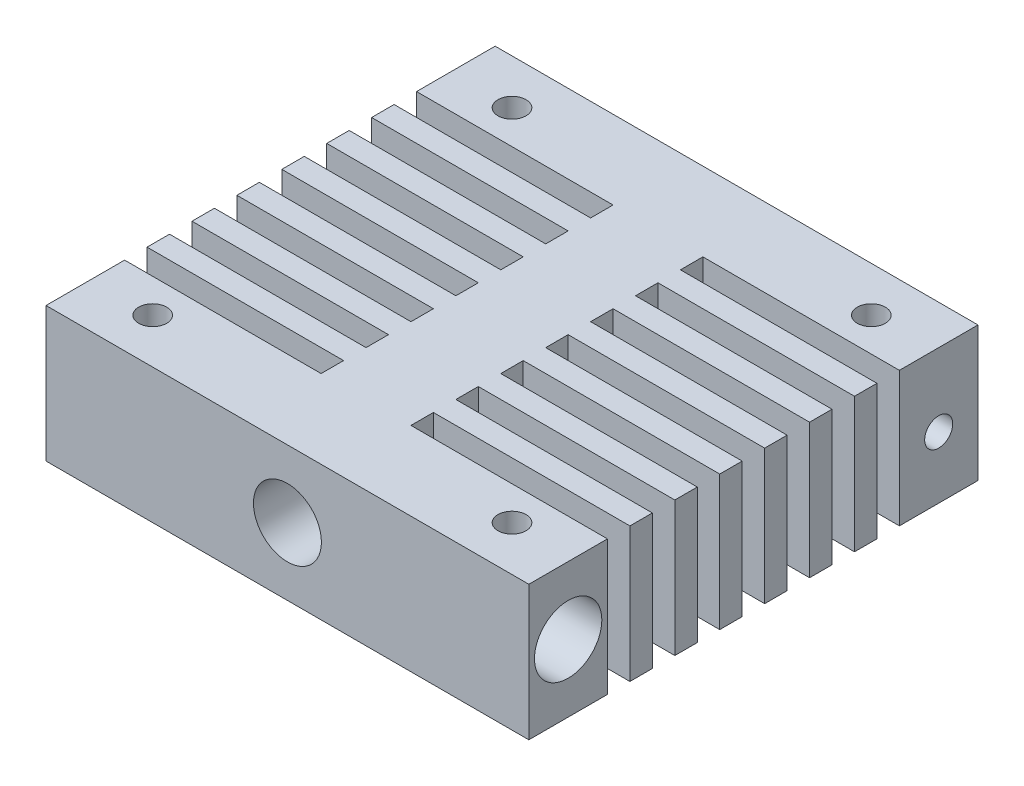
SolidWorks part; units mm, degrees
material "6063-O"
ref_plane "前视基准面" through (0, 0, 0) normal (0, 0, 1) x (1, 0, 0)
ref_plane "上视基准面" through (0, 0, 0) normal (0, 1, 0) x (1, 0, 0)
ref_plane "右视基准面" through (0, 0, 0) normal (1, 0, 0) x (0, 0, -1)
sketch "草图1" plane through (0, 0, 0) normal (0, 1, 0) x (1, 0, 0)
  line L0 (-123.0659, 0) -> (151.55, 0) construction
  line L1 (0, 104.9894) -> (0, -121.0574) construction
  line L2 (-21.5, 20) -> (-21.5, -20)
  line L3 (-21.5, -20) -> (21.5, -20)
  line L4 (21.5, -20) -> (21.5, 20)
  line L5 (21.5, 20) -> (-21.5, 20)
  dimension "D1" = 43
  dimension "D2" = 40
extrude "凸台-拉伸1" add sketch "草图1" along normal blind 2
sketch "草图2" plane through (0, 0, 0) normal (0, 1, 0) x (1, 0, 0)
  line L0 (51.1159, 0) -> (-53.8356, 0) construction
  line L1 (0, 43.0666) -> (0, -46.7433) construction
  line L2 (6, 20) -> (6, 16.51)
  line L3 (21.5, 20) -> (-21.5, 20) construction
  line L4 (6, 16.51) -> (-6, 16.51)
  line L5 (-6, 16.51) -> (-6, 20)
  line L6 (-6, 20) -> (6, 20)
  line L7 (-6, -20) -> (6, -20)
  line L8 (-6, -16.51) -> (-6, -20)
  line L9 (6, -16.51) -> (-6, -16.51)
  line L10 (6, -20) -> (6, -16.51)
  dimension "D1" = 12
  dimension "D2" = 33.02
extrude "凸台-拉伸2" [suppressed] add sketch "草图2" against normal blind 3
chamfer "倒角1" [suppressed] distance 0.5 angle 45
chamfer "倒角2" [suppressed] distance 0.2 angle 45
sketch "草图3" plane through (0, 2, 0) normal (0, 1, 0) x (1, 0, 0)
  line L0 (0, 34.8618) -> (0, -39.6513) construction
  line L1 (-44.5227, 0) -> (51.9212, 0) construction
  line L2 (-21.5, 20) -> (-21.5, -20)
  line L3 (-21.5, -20) -> (21.5, -20)
  line L4 (21.5, -20) -> (21.5, 20)
  line L5 (21.5, 20) -> (-21.5, 20)
  line L7 (21.5, 20) -> (-21.5, 20) construction
  line L8 (-21.5, -20) -> (21.5, -20) construction
  dimension "D1" = 43
extrude "凸台-拉伸3" add sketch "草图3" along normal blind 10
sketch "草图4" plane through (0, 0, 20) normal (0, 0, 1) x (1, 0, 0)
  circle A0 centre (0, 6) radius 3.025
  dimension "D2" = 6.05
  dimension "D1" = 6
extrude "切除-拉伸1" cut sketch "草图4" against normal blind 20
sketch "草图5" plane through (0, 0, -20) normal (0, 0, -1) x (-1, 0, 0)
  circle A0 centre (0, 6) radius 2.025
  dimension "D1" = 4.05
extrude "切除-拉伸2" cut sketch "草图5" against normal up to next
hole_wizard "M6 螺纹孔1" positions "草图6" profile "草图7" tap size "M6" standard "GB"
sketch "草图6" plane through (0, 0, -20) normal (0, 0, -1) x (-1, 0, 0)
  point P0 (0, 6)
sketch "草图7" plane through (0, 6, -20) normal (1, 0, 0) x (0, 1, 0)
  line L0 (0, 0) -> (0, 8)
  line L1 (0, 8) -> (2.5, 8)
  line L2 (2.5, 8) -> (2.5, 0)
  line L5 (2.5, 0) -> (0, 0)
  line L10 (0, 8) -> (-2.5, 8) construction
  line L11 (0, -6.35) -> (0, 107.95) construction
  dimension "螺纹孔钻头直径" = 5
  dimension "螺纹孔钻头深度" = 8
  dimension "导头角度" = 180
cosmetic thread "孔螺蚊线1" parameters "D1"=8, "D2"=6
sketch "草图8" plane through (0, 12, 0) normal (0, 1, 0) x (1, 0, 0)
  line L0 (-21.5, -13) -> (-4, -13)
  line L1 (-4, -13) -> (-4, -11)
  line L2 (-4, -11) -> (-21.5, -11)
  line L3 (-21.5, -11) -> (-21.5, -13)
  line L4 (0, 25.0591) -> (0, -36.4121) construction
  line L6 (-21.5, -20) -> (21.5, -20) construction
  line L7 (-21.5, -9) -> (-4, -9)
  line L8 (-4, -7) -> (-21.5, -7)
  line L9 (-21.5, -7) -> (-21.5, -9)
  line L10 (-4, -9) -> (-4, -7)
  line L11 (-21.5, -5) -> (-4, -5)
  line L12 (-4, -3) -> (-21.5, -3)
  line L13 (-21.5, -3) -> (-21.5, -5)
  line L14 (-4, -5) -> (-4, -3)
  line L15 (-21.5, -1) -> (-4, -1)
  line L16 (-4, 1) -> (-21.5, 1)
  line L17 (-21.5, 1) -> (-21.5, -1)
  line L18 (-4, -1) -> (-4, 1)
  line L19 (-21.5, 3) -> (-4, 3)
  line L20 (-4, 5) -> (-21.5, 5)
  line L21 (-21.5, 5) -> (-21.5, 3)
  line L22 (-4, 3) -> (-4, 5)
  line L23 (-21.5, 7) -> (-4, 7)
  line L24 (-4, 9) -> (-21.5, 9)
  line L25 (-21.5, 9) -> (-21.5, 7)
  line L26 (-4, 7) -> (-4, 9)
  line L27 (-21.5, 11) -> (-4, 11)
  line L28 (-4, 13) -> (-21.5, 13)
  line L29 (-21.5, 13) -> (-21.5, 11)
  line L30 (-4, 11) -> (-4, 13)
  line L31 (4, 11) -> (4, 13)
  line L32 (21.5, 13) -> (21.5, 11)
  line L33 (4, 13) -> (21.5, 13)
  line L34 (21.5, 11) -> (4, 11)
  line L35 (-21.5, 20) -> (-21.5, -20) construction
  line L45 (4, 7) -> (4, 9)
  line L46 (21.5, 9) -> (21.5, 7)
  line L47 (4, 9) -> (21.5, 9)
  line L48 (21.5, 7) -> (4, 7)
  line L49 (4, 3) -> (4, 5)
  line L50 (21.5, 5) -> (21.5, 3)
  line L51 (4, 5) -> (21.5, 5)
  line L52 (21.5, 3) -> (4, 3)
  line L53 (4, -1) -> (4, 1)
  line L54 (21.5, 1) -> (21.5, -1)
  line L55 (4, 1) -> (21.5, 1)
  line L56 (21.5, -1) -> (4, -1)
  line L57 (4, -5) -> (4, -3)
  line L58 (21.5, -3) -> (21.5, -5)
  line L59 (4, -3) -> (21.5, -3)
  line L60 (21.5, -5) -> (4, -5)
  line L61 (4, -9) -> (4, -7)
  line L62 (21.5, -7) -> (21.5, -9)
  line L63 (4, -7) -> (21.5, -7)
  line L64 (21.5, -9) -> (4, -9)
  line L65 (21.5, -11) -> (21.5, -13)
  line L66 (4, -11) -> (21.5, -11)
  line L67 (4, -13) -> (4, -11)
  line L68 (21.5, -13) -> (4, -13)
  dimension "D1" = 2
  dimension "D2" = 7
  dimension "D3" = 8
  dimension "D5" = 2
  dimension "D4" = 7
extrude "切除-拉伸3" cut sketch "草图8" against normal up to surface (12 mm away) up to face at (0, 0, 0)
hole_wizard "M3 螺纹孔1" positions "草图9" profile "草图10" tap size "M3" standard "GB" end condition through all
sketch "草图9" plane through (0, 12, 0) normal (0, 1, 0) x (1, 0, 0)
  point P0 (-16, 16)
  point P2 (16, 16)
  point P6 (-16, -16)
  point P16 (16, -16)
  dimension "D1" = 16
  dimension "D2" = 16
  dimension "D3" = 16
  dimension "D4" = 16
cosmetic thread "孔螺蚊线11" parameters "D2"=3
cosmetic thread "孔螺蚊线12" parameters "D2"=3
cosmetic thread "孔螺蚊线13" parameters "D2"=3
cosmetic thread "孔螺蚊线14" parameters "D2"=3
sketch "草图10" plane through (-16, 12, -16) normal (1, 0, 0) x (0, 0, 1)
  line L0 (0, 0) -> (0, 12)
  line L1 (0, 12) -> (1.25, 12)
  line L2 (1.25, 12) -> (1.25, 0)
  line L5 (1.25, 0) -> (0, 0)
  line L11 (0, -6.35) -> (0, 107.95) construction
  dimension "通孔螺纹孔钻头直径" = 2.5
  dimension "通孔螺纹孔钻头深度" = 12
hole_wizard "M3 螺纹孔2" positions "草图12" profile "草图13" tap size "M3" standard "GB"
sketch "草图12" plane through (21.5, 0, 0) normal (1, 0, 0) x (0, 0, -1)
  line L2 (20, 12) -> (20, 0) construction
  line L3 (13, 0) -> (20, 0) construction
  point P0 (16.5, 5.5)
  dimension "D1" = 3.5
  dimension "D2" = 5.5
sketch "草图13" plane through (21.5, 5.5, -16.5) normal (0, 1, 0) x (0, 0, -1)
  line L0 (0, 0) -> (0, 4)
  line L1 (0, 4) -> (1.25, 4)
  line L2 (1.25, 4) -> (1.25, 0)
  line L5 (1.25, 0) -> (0, 0)
  line L10 (0, 4) -> (-1.25, 4) construction
  line L11 (0, -6.35) -> (0, 107.95) construction
  dimension "螺纹孔钻头直径" = 2.5
  dimension "螺纹孔钻头深度" = 4
  dimension "导头角度" = 180
cosmetic thread "孔螺蚊线6" parameters "D1"=4, "D2"=3
hole_wizard "M3 螺纹孔3" positions "草图14" profile "草图15" tap size "M3" standard "GB"
sketch "草图14" plane through (-21.5, 0, 0) normal (-1, 0, 0) x (0, 0, 1)
  line L3 (-20, 12) -> (-20, 0) construction
  line L4 (-20, 0) -> (-13, 0) construction
  line L5 (13, 0) -> (20, 0) construction
  line L6 (20, 12) -> (20, 0) construction
  point P0 (-16.5, 5.5)
  point P8 (16.5, 5.5)
  dimension "D1" = 3.5
  dimension "D2" = 5.5
  dimension "D3" = 5.5
  dimension "D4" = 3.5
sketch "草图15" plane through (-21.5, 5.5, -16.5) normal (0, 1, 0) x (0, 0, 1)
  line L0 (0, 0) -> (0, 4)
  line L1 (0, 4) -> (1.25, 4)
  line L2 (1.25, 4) -> (1.25, 0)
  line L5 (1.25, 0) -> (0, 0)
  line L10 (0, 4) -> (-1.25, 4) construction
  line L11 (0, -6.35) -> (0, 107.95) construction
  dimension "螺纹孔钻头直径" = 2.5
  dimension "螺纹孔钻头深度" = 4
  dimension "导头角度" = 180
cosmetic thread "孔螺蚊线7" parameters "D1"=4, "D2"=3
cosmetic thread "孔螺蚊线16" parameters "D1"=4, "D2"=3
sketch "草图16" plane through (21.5, 0, 0) normal (1, 0, 0) x (0, 0, -1)
  line L3 (-20, 0) -> (-13, 0) construction
  line L4 (-20, 12) -> (-20, 0) construction
  circle A0 centre (-16.5, 6) radius 3
  dimension "D1" = 6
  dimension "D2" = 6
  dimension "D3" = 3.5
extrude "切除-拉伸4" cut sketch "草图16" against normal blind 13.5
hole_wizard "M3 螺纹孔4" positions "草图17" profile "草图18" tap size "M3" standard "GB"
sketch "草图17" plane through (8, 0, 0) normal (1, 0, 0) x (0, 0, -1)
  point P0 (-16.5, 6)
sketch "草图18" plane through (8, 6, 16.5) normal (0, 1, 0) x (0, 0, -1)
  line L0 (0, 0) -> (0, 4.975)
  line L1 (0, 4.975) -> (1.25, 4.975)
  line L2 (1.25, 4.975) -> (1.25, 0)
  line L5 (1.25, 0) -> (0, 0)
  line L11 (0, -6.35) -> (0, 107.95) construction
  dimension "通孔螺纹孔钻头直径" = 2.5
  dimension "通孔螺纹孔钻头深度" = 4.975
cosmetic thread "孔螺蚊线15" parameters "D2"=3
hole_wizard "M3 螺纹孔5" [suppressed] positions "草图19" profile "草图20" tap size "M3" standard "GB"
sketch "草图19" plane through (0, 0, 0) normal (0, -1, 0) x (-1, 0, 0)
  line L0 (0, 104.9894) -> (0, -121.0574) construction
  line L1 (123.0659, 0) -> (-151.55, 0) construction
  line L2 (0, 104.9894) -> (0, -121.0574) construction
  line L3 (123.0659, 0) -> (-151.55, 0) construction
  point P0 (-16, 16.5)
  point P2 (16, 16.5)
  point P4 (16, -16.5)
  point P6 (-16, -16.5)
  dimension "D1" = 32
  dimension "D2" = 33
sketch "草图20" plane through (16, 0, -16.5) normal (1, 0, 0) x (0, 0, -1)
  line L0 (0, 0) -> (0, 4.7511)
  line L1 (0, 4.7511) -> (1.25, 4)
  line L2 (1.25, 4) -> (1.25, 0)
  line L5 (1.25, 0) -> (0, 0)
  line L10 (0, 4.7511) -> (-1.25, 4) construction
  line L11 (0, -6.35) -> (0, 107.95) construction
  dimension "螺纹孔钻头直径" = 2.5
  dimension "螺纹孔钻头深度" = 4
  dimension "导头角度" = 118
cosmetic thread "孔螺蚊线17" [suppressed] parameters "D1"=3.4222, "D2"=3
cosmetic thread "孔螺蚊线18" [suppressed] parameters "D1"=4, "D2"=3
cosmetic thread "孔螺蚊线19" [suppressed] parameters "D1"=4, "D2"=3
cosmetic thread "孔螺蚊线20" [suppressed] parameters "D1"=4, "D2"=3
